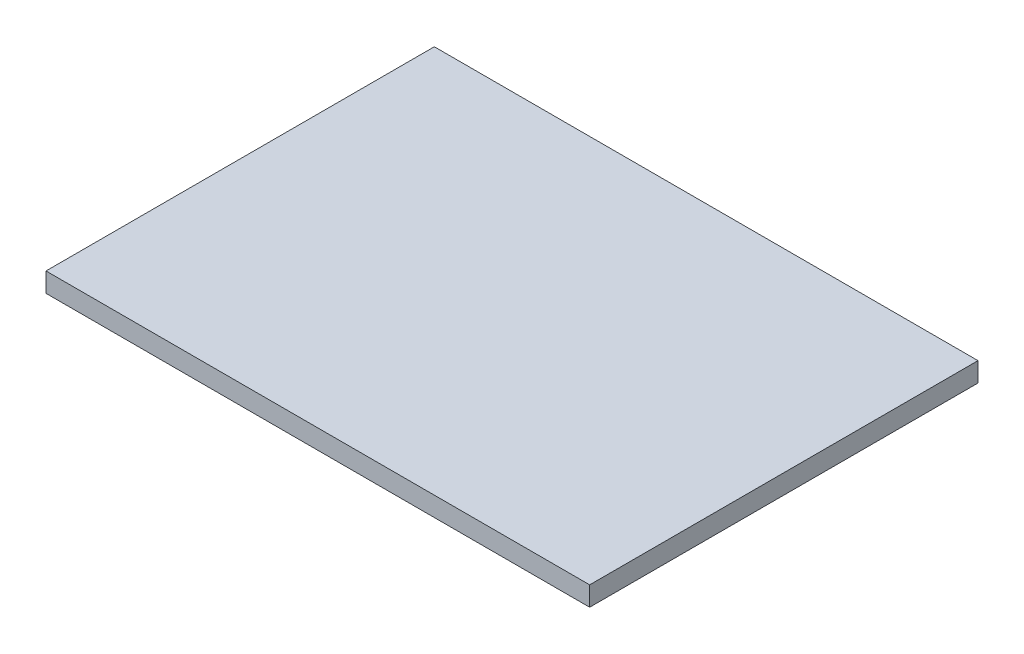
SolidWorks part; units mm, degrees
material "Alloy Steel (SS)"
ref_plane "Front Plane" through (0, 0, 0) normal (0, 0, 1) x (1, 0, 0)
ref_plane "Top Plane" through (0, 0, 0) normal (0, 1, 0) x (1, 0, 0)
ref_plane "Right Plane" through (0, 0, 0) normal (1, 0, 0) x (0, 0, -1)
sketch "Sketch1" plane through (0, 0, 0) normal (0, 1, 0) x (1, 0, 0)
  line L1 (-175.7216, 120.2519) -> (535.4784, 120.2519)
  line L2 (-175.7216, 120.2519) -> (-175.7216, -387.7481)
  line L3 (-175.7216, -387.7481) -> (535.4784, -387.7481)
  line L4 (535.4784, 120.2519) -> (535.4784, -387.7481)
  dimension "D1" = 711.2
  dimension "D2" = 508
  dimension "D3" = 535.4784
  dimension "D4" = 120.2519
extrude "Boss-Extrude1" add sketch "Sketch1" along normal blind 25.4
